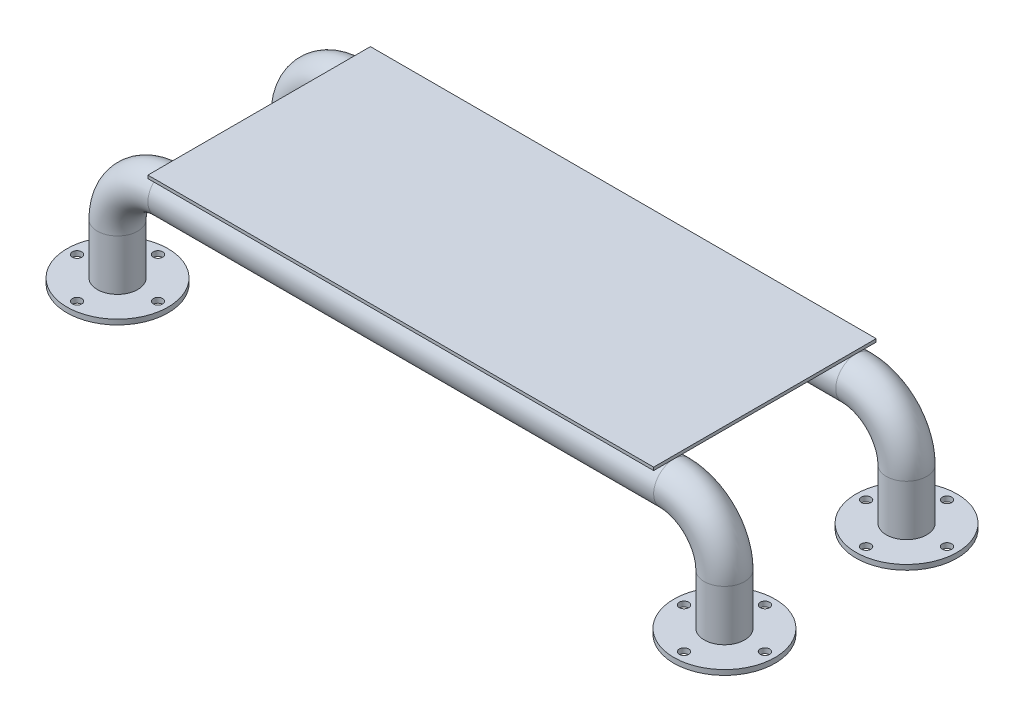
SolidWorks part; units mm, degrees
ref_plane "Front Plane" through (0, 0, 0) normal (0, 0, 1) x (1, 0, 0)
ref_plane "Top Plane" through (0, 0, 0) normal (0, 1, 0) x (1, 0, 0)
ref_plane "Right Plane" through (0, 0, 0) normal (1, 0, 0) x (0, 0, -1)
sketch "Sketch1" plane through (0, 0, 0) normal (0, 0, 1) x (1, 0, 0)
  line L0 (250, 0) -> (-250, 0)
  line L1 (-300, -50) -> (-300, -100)
  line L2 (0, 0) -> (0, 399.0621) construction
  line L3 (300, -50) -> (300, -100)
  arc A0 (250, 0) -> (300, -50) centre (250, -50) cw
  arc A1 (-250, 0) -> (-300, -50) centre (-250, -50) ccw
  point P9 (300, 0)
  point P12 (-300, 0)
  dimension "D3" = 50
  dimension "D1" = 600
  dimension "D2" = 100
sketch "Sketch2" plane through (0, 0, 0) normal (1, 0, 0) x (0, 0, -1)
  circle A0 centre (0, 0) radius 20
  dimension "D1" = 40
sweep "Sweep1" add profiles "Sketch2" path "Sketch1"
ref_plane "Plane1" through (0, 0, 180) normal (0, 0, 1) x (1, 0, 0)
sketch "Sketch3" plane through (0, 0, 180) normal (0, 0, 1) x (1, 0, 0)
  line L0 (250, 0) -> (-250, 0)
  line L1 (-300, -100) -> (-300, -50)
  line L3 (-300, -100) -> (-300, -50) construction
  line L4 (-320, -100) -> (-280, -100) construction
  line L5 (-320, -50) -> (-280, -50) construction
  line L6 (0, 0) -> (0, 102.1219) construction
  line L7 (300, -100) -> (300, -50)
  arc A1 (300, -50) -> (250, 0) centre (250, -50) ccw
  arc A2 (-300, -50) -> (-250, 0) centre (-250, -50) cw
  point P17 (300, 0)
  point P20 (-300, 0)
  dimension "D1" = 50
sketch "Sketch4" plane through (0, 0, 0) normal (1, 0, 0) x (0, 0, -1)
  circle A0 centre (-180, 0) radius 20
  dimension "D1" = 40
sweep "Sweep2" add profiles "Sketch4" path "Sketch3"
sketch "Sketch5" plane through (0, -100, 0) normal (0, -1, 0) x (1, 0, 0)
  circle A0 centre (-300, 180) radius 50
  circle A1 centre (-300, 0) radius 50
  circle A2 centre (300, 0) radius 50
  circle A3 centre (300, 180) radius 50
  point P3 (0, 0)
  dimension "D1" = 100
extrude "Boss-Extrude1" add sketch "Sketch5" along normal blind 5
ref_plane "Plane2" through (100, 0, 0) normal (1, 0, 0) x (0, 0, -1)
ref_plane "Plane3" through (-100, 0, 0) normal (1, 0, 0) x (0, 0, -1)
ref_plane "Plane4" through (0, 0, 100) normal (0, 0, 1) x (1, 0, 0)
sketch "Sketch8" plane through (0, 0, 100) normal (0, 0, 1) x (1, 0, 0)
  line L0 (-100, -68.75) -> (-100, 68.75) construction
  line L1 (100, -68.75) -> (100, 68.75) construction
  circle A0 centre (-100, 0) radius 20
  circle A1 centre (100, 0) radius 20
extrude "Boss-Extrude2" add sketch "Sketch8" along normal up to next and the other way up to next
ref_plane "Plane5" through (0, 20, 0) normal (0, 1, 0) x (1, 0, 0)
sketch "Sketch10" plane through (0, 20, 0) normal (0, 1, 0) x (1, 0, 0)
  line L1 (-250, 20) -> (250, 20)
  line L2 (-250, 20) -> (-250, -200)
  line L3 (-250, -200) -> (250, -200)
  line L4 (250, 20) -> (250, -200)
extrude "Boss-Extrude3" add sketch "Sketch10" along normal blind 3 separate body
sketch "Sketch11" plane through (0, -105, 0) normal (0, -1, 0) x (1, 0, 0)
  line L0 (0, 200) -> (0, -20) construction
  line L1 (-250, 200) -> (250, 200) construction
  line L2 (-250, -20) -> (250, -20) construction
  line L3 (-250, 90) -> (250, 90) construction
  line L4 (-250, -20) -> (-250, 200) construction
  line L5 (250, 200) -> (250, -20) construction
  circle A0 centre (-300, 180) radius 40 construction
  circle A1 centre (-300, 220) radius 4.6757
  circle A2 centre (-260, 180) radius 4.6757
  circle A3 centre (-300, 140) radius 4.6757
  circle A4 centre (-340, 180) radius 4.6757
  circle A5 centre (260, 180) radius 4.6757
  circle A6 centre (300, 140) radius 4.6757
  circle A7 centre (300, 180) radius 40 construction
  circle A8 centre (340, 180) radius 4.6757
  circle A9 centre (300, 220) radius 4.6757
  circle A10 centre (-300, 0) radius 40 construction
  circle A11 centre (-340, 0) radius 4.6757
  circle A12 centre (-300, 40) radius 4.6757
  circle A13 centre (-260, 0) radius 4.6757
  circle A14 centre (-300, -40) radius 4.6757
  circle A15 centre (300, 0) radius 40 construction
  circle A16 centre (300, -40) radius 4.6757
  circle A17 centre (340, 0) radius 4.6757
  circle A18 centre (300, 40) radius 4.6757
  circle A19 centre (260, 0) radius 4.6757
  point P26 (-300, 180)
  dimension "D1" = 80
  dimension "D2" = 4
extrude "Cut-Extrude1" cut sketch "Sketch11" against normal blind 5
